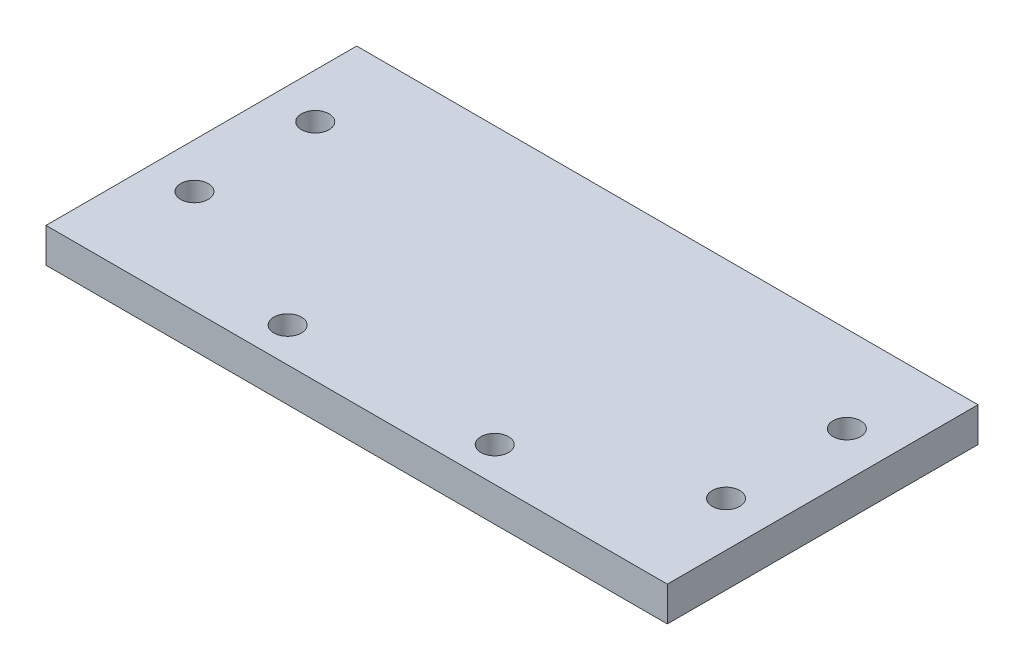
SolidWorks part; units mm, degrees
ref_plane "Front Plane" through (0, 0, 0) normal (0, 0, 1) x (1, 0, 0)
ref_plane "Top Plane" through (0, 0, 0) normal (0, 1, 0) x (1, 0, 0)
ref_plane "Right Plane" through (0, 0, 0) normal (1, 0, 0) x (0, 0, -1)
sketch "Sketch1" plane through (0, 0, 0) normal (0, 1, 0) x (1, 0, 0)
  line L0 (0, 0) -> (0, 32.9687) construction
  line L1 (-90, -45) -> (90, -45)
  line L2 (-90, -45) -> (-90, 45)
  line L3 (-90, 45) -> (90, 45)
  line L4 (90, -45) -> (90, 45)
  line L5 (-90, -45) -> (90, 45) construction
  line L6 (-90, 45) -> (90, -45) construction
  line L7 (0, 32.9687) -> (0, 0) construction
  line L9 (5.5376, -35) -> (-30, -35) construction
  line L10 (-30, -35) -> (49.1996, -35) construction
  circle A0 centre (-77, 20) radius 4
  circle A1 centre (-77, -15) radius 4
  circle A2 centre (-30, -35) radius 4
  circle A3 centre (77, 20) radius 4
  circle A4 centre (77, -15) radius 4
  circle A5 centre (30, -35) radius 4
  point P0 (0, 0)
  point P9 (77, -15)
  point P23 (66.4505, 18.3723)
  point P24 (77, 20)
  point P25 (0, 0)
  dimension "D3" = 35
  dimension "D4" = 8
  dimension "D1" = 90
  dimension "D2" = 180
  dimension "D5" = 13
  dimension "D6" = 60
  dimension "D7" = 10
  dimension "D8" = 30
extrude "Boss-Extrude1" add sketch "Sketch1" along normal blind 10
